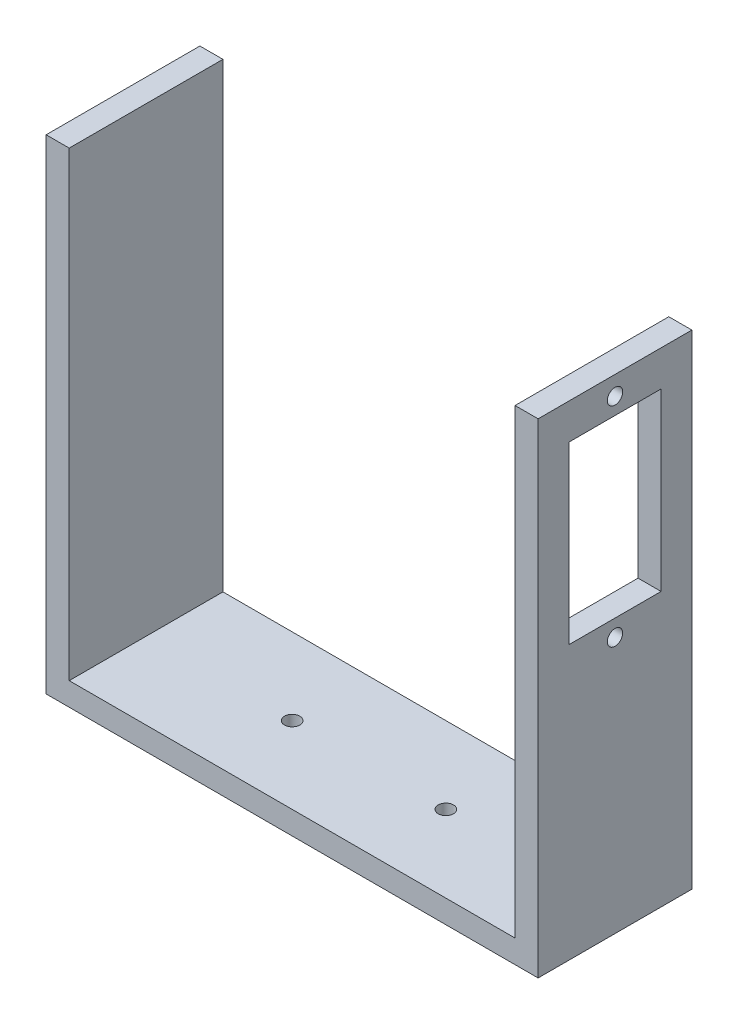
SolidWorks part; units mm, degrees
ref_plane "Front Plane" through (0, 0, 0) normal (0, 0, 1) x (1, 0, 0)
ref_plane "Top Plane" through (0, 0, 0) normal (0, 1, 0) x (1, 0, 0)
ref_plane "Right Plane" through (0, 0, 0) normal (1, 0, 0) x (0, 0, -1)
sketch "Sketch1" plane through (0, 0, 0) normal (0, 0, 1) x (1, 0, 0)
  line L0 (0, 0) -> (58, 0)
  line L1 (58, 0) -> (58, 60)
  line L2 (58, 60) -> (61, 60)
  line L3 (61, 60) -> (61, -3)
  line L4 (61, -3) -> (-3, -3)
  line L5 (0, 0) -> (0, 60)
  line L6 (0, 60) -> (-3, 60)
  line L7 (-3, 60) -> (-3, -3)
extrude "Boss-Extrude1" add sketch "Sketch1" against normal blind 20 contours L3 L4 L7 L6 L5 L0 L1 L2
sketch "Sketch3" plane through (61, 0, 0) normal (1, 0, 0) x (0, 0, -1)
  line L6 (10, 32.55) -> (16, 32.55)
  line L7 (10, 55.3661) -> (16, 55.3661)
  line L8 (16, 55.3661) -> (16, 32.55)
  line L9 (10, 55.3661) -> (4, 55.3661)
  line L10 (4, 55.3661) -> (4, 32.55)
  line L11 (4, 32.55) -> (10, 32.55)
  circle A0 centre (10, 57.5411) radius 1
  circle A1 centre (10, 30.375) radius 1
extrude "Cut-Extrude1" cut sketch "Sketch3" against normal blind 10
sketch "Sketch4" plane through (0, 0, 0) normal (0, 1, 0) x (1, 0, 0)
  line L1 (0, 0) -> (29, 0)
  line L2 (0, 0) -> (58, 0) construction
  circle A0 centre (39, 10) radius 1
  circle A1 centre (19, 10) radius 1
extrude "Cut-Extrude2" cut sketch "Sketch4" against normal blind 10 contours A1 | A0
